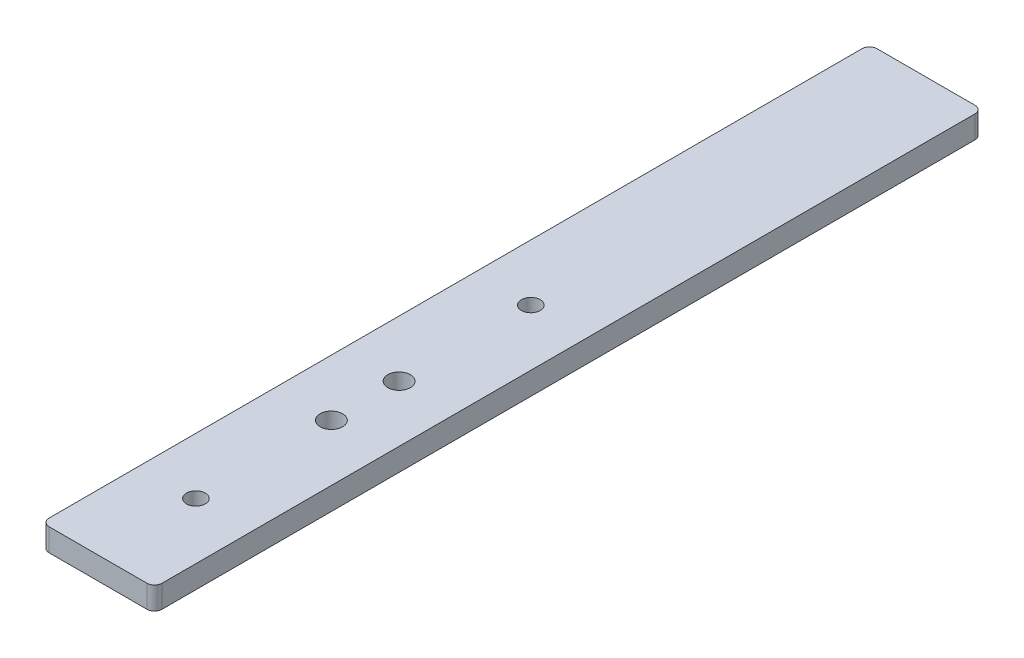
SolidWorks part; units mm, degrees
ref_plane "前视基准面" through (0, 0, 0) normal (0, 0, 1) x (1, 0, 0)
ref_plane "上视基准面" through (0, 0, 0) normal (0, 1, 0) x (1, 0, 0)
ref_plane "右视基准面" through (0, 0, 0) normal (1, 0, 0) x (0, 0, -1)
other "Configuration Table"
sketch "草图1" plane through (0, 0, 0) normal (0, 1, 0) x (1, 0, 0)
  line L1 (0, 0) -> (15, 0)
  line L2 (0, 0) -> (0, 110)
  line L3 (0, 110) -> (15, 110)
  line L4 (15, 0) -> (15, 110)
  dimension "D1" = 15
  dimension "D2" = 110
extrude "凸台-拉伸1" add sketch "草图1" along normal blind 3
fillet "圆角1" radius 1 4 edges at (15, 1.5, -110) (0, 1.5, -110) (15, 1.5, 0) (0, 1.5, 0)
sketch "草图2" plane through (0, 3, 0) normal (0, 1, 0) x (1, 0, 0)
  line L0 (7.5, 0) -> (7.5, 110) construction
  line L1 (1, 0) -> (14, 0) construction
  line L2 (14, 110) -> (1, 110) construction
  circle A0 centre (7.5, 13) radius 1.25
  circle A1 centre (7.5, 57.5) radius 1.25
  dimension "D2" = 2.5
  dimension "D3" = 2.5
  dimension "D1" = 13
  dimension "D4" = 44.5
extrude "切除-拉伸1" cut sketch "草图2" against normal blind 3
sketch "草图3" plane through (0, 3, 0) normal (0, 1, 0) x (1, 0, 0)
  line L0 (0, 109) -> (0, 1) construction
  line L1 (0, 45.5) -> (15, 45.5) construction
  line L2 (0, 45.5) -> (0, 25.5) construction
  line L3 (0, 25.5) -> (15, 25.5) construction
  line L4 (15, 45.5) -> (15, 25.5) construction
  line L5 (15, 1) -> (15, 109) construction
  line L6 (1, 0) -> (14, 0) construction
  line L7 (0, 35.5) -> (15, 35.5) construction
  line L8 (7.5, 45.5) -> (7.5, 25.5) construction
  circle A0 centre (7.5, 40) radius 1.5
  circle A1 centre (7.5, 31) radius 1.5
  dimension "D3" = 3
  dimension "D4" = 3
  dimension "D1" = 25.5
  dimension "D2" = 20
  dimension "D5" = 9
  dimension "D6" = 4.5
extrude "切除-拉伸2" cut sketch "草图3" against normal blind 10
